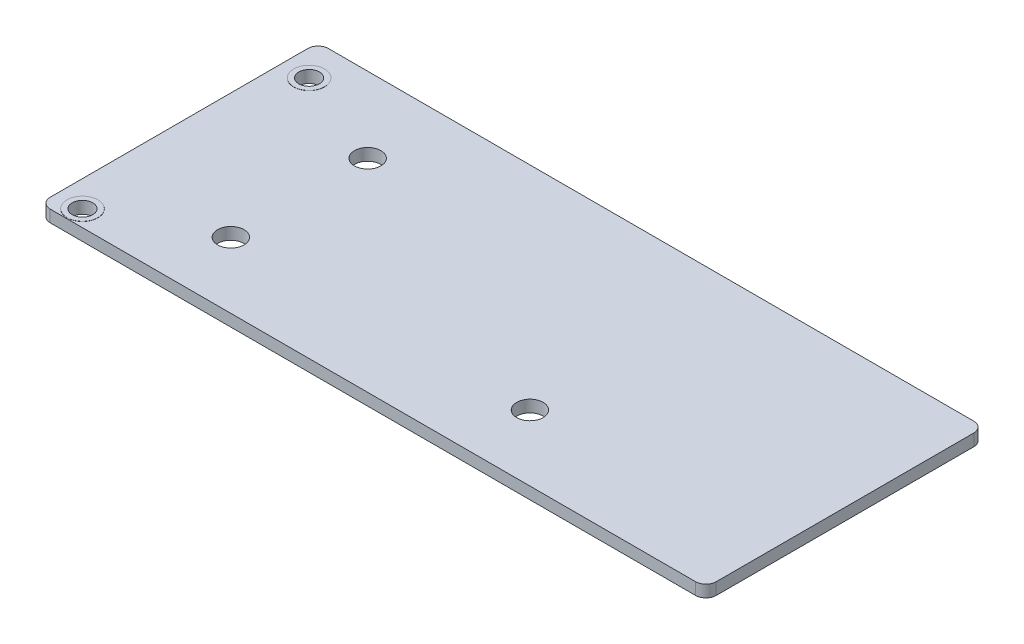
SolidWorks part; units mm, degrees
ref_plane "Front Plane" through (0, 0, 0) normal (0, 0, 1) x (1, 0, 0)
ref_plane "Top Plane" through (0, 0, 0) normal (0, 1, 0) x (1, 0, 0)
ref_plane "Right Plane" through (0, 0, 0) normal (1, 0, 0) x (0, 0, -1)
sketch "Sketch1" plane through (0, 0, 0) normal (0, 1, 0) x (1, 0, 0)
  line L1 (-32.325, -13.5) -> (32.325, -13.5)
  line L2 (-32.325, -13.5) -> (-32.325, 13.5)
  line L3 (-32.325, 13.5) -> (32.325, 13.5)
  line L4 (32.325, -13.5) -> (32.325, 13.5)
  line L5 (-32.325, -13.5) -> (32.325, 13.5) construction
  line L6 (-32.325, 13.5) -> (32.325, -13.5) construction
  point P0 (0, 0)
  dimension "D1" = 64.65
  dimension "D2" = 27
extrude "Boss-Extrude1" add sketch "Sketch1" along normal blind 1.16
fillet "Fillet1" radius 1 4 edges at (-32.325, 0.58, -13.5) (32.325, 0.58, -13.5) (32.325, 0.58, 13.5) (-32.325, 0.58, 13.5)
sketch "Sketch2" plane through (0, 1.16, 0) normal (0, 1, 0) x (1, 0, 0)
  line L0 (31.325, 13.5) -> (-31.325, 13.5) construction
  line L1 (-32.325, 12.5) -> (-32.325, -12.5) construction
  line L2 (-31.325, -13.5) -> (31.325, -13.5) construction
  line L3 (-20.19, -7.105) -> (-20.19, 6.18) construction
  line L4 (-20.19, -7.105) -> (8.845, -7.105) construction
  circle A0 centre (-29.775, -11.92) radius 1
  circle A1 centre (-29.775, 10.08) radius 1
  circle A3 centre (-20.19, -7.105) radius 1.285
  circle A4 centre (-20.19, 6.18) radius 1.285
  circle A5 centre (8.845, -7.105) radius 1.285
  dimension "D1" = 2
  dimension "D6" = 2.57
  dimension "D2" = 3.42
  dimension "D3" = 2.55
  dimension "D4" = 2.55
  dimension "D5" = 1.58
  dimension "D7" = 13.285
  dimension "D8" = 29.035
  dimension "D9" = 20.605
  dimension "D10" = 12.135
extrude "Cut-Extrude1" cut sketch "Sketch2" against normal through all
sketch "Sketch3" plane through (0, 1.16, 0) normal (0, 1, 0) x (1, 0, 0)
  circle A0 centre (-29.775, -11.92) radius 1.5
  circle A1 centre (-29.775, 10.08) radius 1.5
  circle A2 centre (-29.775, -11.92) radius 1
  circle A3 centre (-29.775, 10.08) radius 1
  circle A4 centre (-29.775, -11.92) radius 1 construction
  dimension "D1" = 3
extrude "Boss-Extrude2" add sketch "Sketch3" along normal blind 0.015 and the other way blind 1.165
